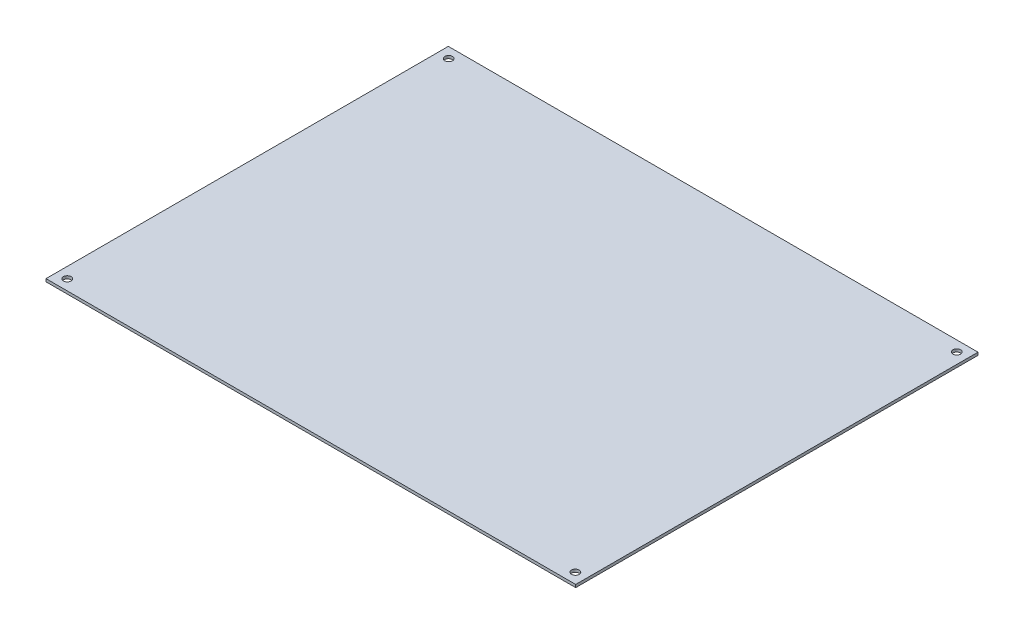
SolidWorks part; units mm, degrees
ref_plane "Front Plane" through (0, 0, 0) normal (0, 0, 1) x (1, 0, 0)
ref_plane "Top Plane" through (0, 0, 0) normal (0, 1, 0) x (1, 0, 0)
ref_plane "Right Plane" through (0, 0, 0) normal (1, 0, 0) x (0, 0, -1)
sketch "Sketch9" plane through (0, 0, 0) normal (0, 1, 0) x (1, 0, 0)
  line L1 (-190.25, 144.5) -> (190.25, 144.5)
  line L2 (-190.25, 144.5) -> (-190.25, -144.5)
  line L3 (-190.25, -144.5) -> (190.25, -144.5)
  line L4 (190.25, 144.5) -> (190.25, -144.5)
extrude "Boss-Extrude2" add sketch "Sketch9" along normal blind 2
sketch "Sketch12" plane through (0, 2, 0) normal (0, 1, 0) x (1, 0, 0)
  point P0 (182.5, 137)
hole_wizard "M5 Clearance Hole1" positions "Sketch13" profile "Sketch14" hole size "M5" standard "ANSI Metric" end condition through all
sketch "Sketch13" plane through (0, 2, 0) normal (0, 1, 0) x (1, 0, 0)
  point P0 (182.5, 137)
sketch "Sketch14" plane through (182.5, 2, -137) normal (1, 0, 0) x (0, 0, 1)
  line L0 (0, 0) -> (0, 2)
  line L1 (0, 2) -> (2.75, 2)
  line L2 (2.75, 2) -> (2.75, 0)
  line L5 (2.75, 0) -> (0, 0)
  line L11 (0, -6.35) -> (0, 107.95) construction
  dimension "Thru Hole Dia." = 5.5
  dimension "Thru Hole Depth" = 2
mirror "Mirror1" about plane through (0, 0, 0) normal (0, 0, 1) of "M5 Clearance Hole1"
mirror "Mirror2" about plane through (0, 0, 0) normal (1, 0, 0) of "Mirror1", "M5 Clearance Hole1"
